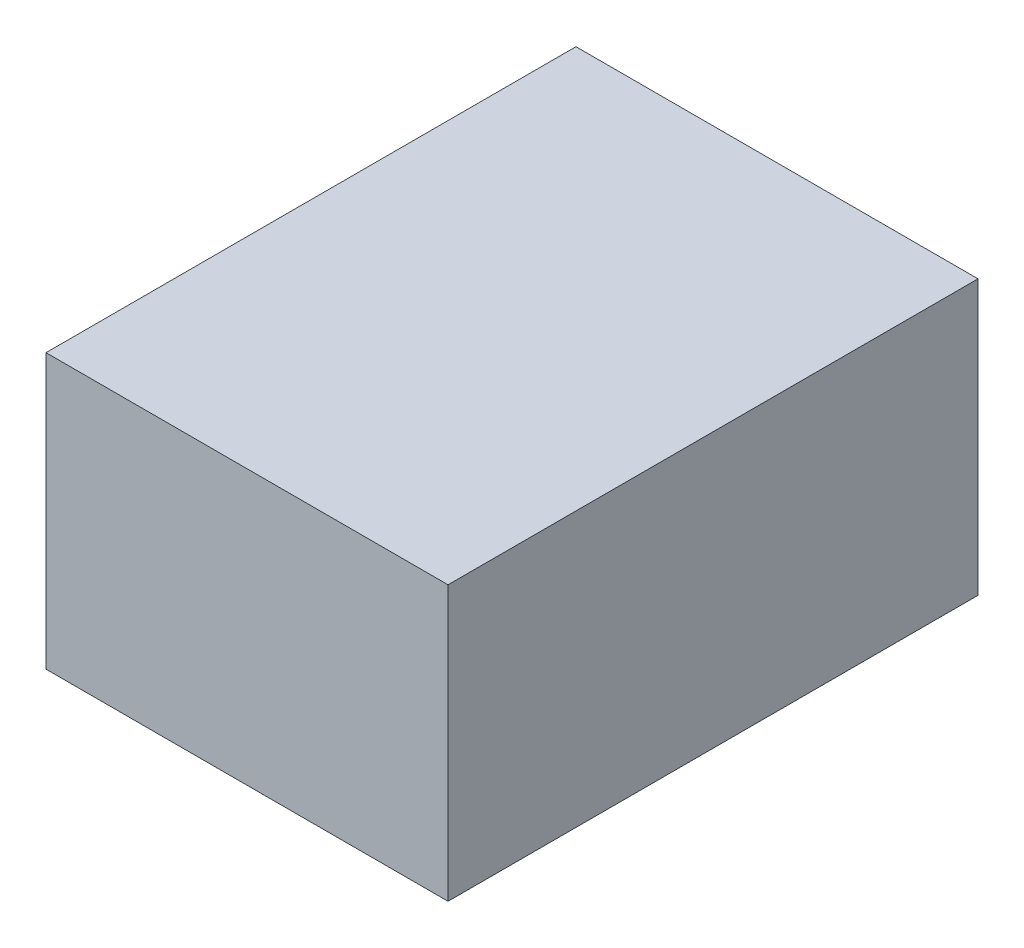
SolidWorks part; units mm, degrees
ref_plane "Front Plane" through (0, 0, 0) normal (0, 0, 1) x (1, 0, 0)
ref_plane "Top Plane" through (0, 0, 0) normal (0, 1, 0) x (1, 0, 0)
ref_plane "Right Plane" through (0, 0, 0) normal (1, 0, 0) x (0, 0, -1)
sketch "Sketch1" plane through (0, 0, 0) normal (0, 1, 0) x (1, 0, 0)
  line L1 (11, -14.5) -> (-11, -14.5)
  line L2 (11, -14.5) -> (11, 14.5)
  line L3 (11, 14.5) -> (-11, 14.5)
  line L4 (-11, -14.5) -> (-11, 14.5)
  line L5 (11, -14.5) -> (-11, 14.5) construction
  line L6 (11, 14.5) -> (-11, -14.5) construction
  point P0 (0, 0)
  dimension "D1" = 29
  dimension "D2" = 22
extrude "Boss-Extrude1" add sketch "Sketch1" along normal blind 15
